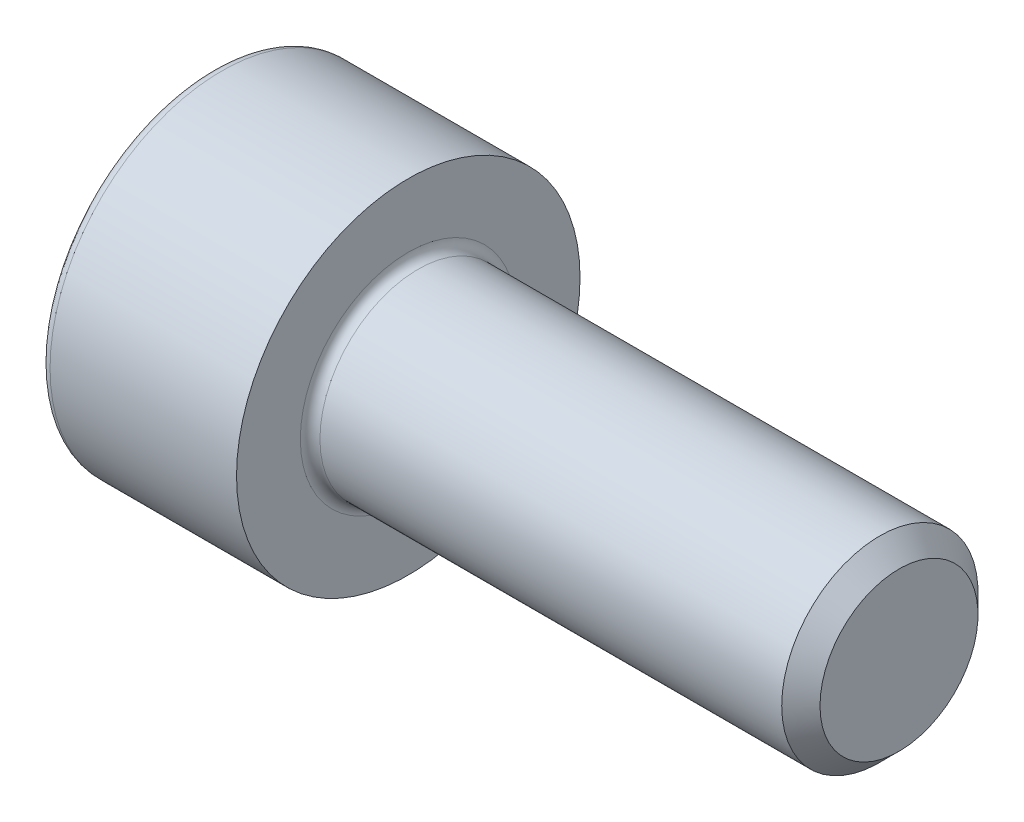
SolidWorks part; units mm, degrees
ref_plane "Front Plane" through (0, 0, 0) normal (0, 0, 1) x (1, 0, 0)
ref_plane "Top Plane" through (0, 0, 0) normal (0, 1, 0) x (1, 0, 0)
ref_plane "Right Plane" through (0, 0, 0) normal (1, 0, 0) x (0, 0, -1)
sketch "BodySke" plane through (0, 0, 0) normal (0, 0, 1) x (1, 0, 0)
  line L0 (0, 0) -> (5.8492, 0) construction
  line L1 (0, 0) -> (0, 3.5)
  line L2 (0, 3.5) -> (4, 3.5)
  line L3 (4, 3.5) -> (4, 2)
  line L4 (4, 2) -> (13.61, 2)
  line L5 (13.61, 2) -> (14, 1.61)
  line L6 (14, 1.61) -> (14, 0)
  line L7 (14, 0) -> (0, 0)
  line L8 (4, 0) -> (4, 0.601) construction
  line L9 (4.7, 1.5877) -> (4.7, 0.9267) construction
  dimension "Body_chamfer_angle" = 45
revolve "BaseBody" add sketch "BodySke" angle 360 about L0
cosmetic thread "ThreadCosmetic" [suppressed] parameters "Thread_length"=10, "Thread_minor"=3.22
fillet "Fillet1" radius 0.2 1 edges at (4, 0, 2)
fillet "Fillet2" radius 0.2 1 edges at (0, 0, 3.5)
sketch "HexSke" plane through (0, 0, 0) normal (1, 0, 0) x (0, 0, -1)
  line L1 (0, 1.7321) -> (-1.5, 0.866)
  line L2 (-1.5, 0.866) -> (-1.5, -0.866)
  line L3 (-1.5, -0.866) -> (0, -1.7321)
  line L4 (0, -1.7321) -> (1.5, -0.866)
  line L5 (1.5, -0.866) -> (1.5, 0.866)
  line L6 (1.5, 0.866) -> (0, 1.7321)
  circle A0 centre (0, 0) radius 1.5 construction
extrude "Hex" cut sketch "HexSke" along normal blind 2
sketch "Hex-PreBroachSke" plane through (0, 0, 0) normal (0, 0, 1) x (1, 0, 0)
  line L0 (0, 0) -> (4.7325, 0) construction
  line L1 (0, 3.3) -> (0, -3.3) construction
  line L2 (0, 0) -> (0, 1.5)
  line L3 (0, 1.5) -> (2, 1.5)
  line L4 (2, 1.5) -> (2.866, 0)
  line L5 (2.866, 0) -> (0, 0)
  dimension "Angle" = 60
revolve "Hex-PreBroach" cut sketch "Hex-PreBroachSke" angle 360 about L0
sketch "ThdSchSke" plane through (0, 0, 0) normal (0, 0, 1) x (1, 0, 0)
  line L0 (0, 0) -> (4.4125, 0) construction
  line L1 (0, 3.3) -> (0, -3.3) construction
  line L2 (12.91, 2.4503) -> (12.91, 2)
  line L3 (12.91, 2.4503) -> (13.3603, 2.4503)
  line L4 (13.3603, 2.4503) -> (13.3603, 2)
  line L5 (13.3603, 2) -> (13.1352, 1.61)
  line L6 (13.1352, 1.61) -> (12.91, 2)
revolve "ThreadSchematic" [suppressed] cut sketch "ThdSchSke" angle 360 about L0
pattern_linear "ThdSchPat" [suppressed]
equation "\"Thread_length@ThreadCosmetic\" = \"Thread_length@BodySke\""
equation "\"Thread_minor@ThreadCosmetic\" = \"Thread_minor@BodySke\""
equation "\"Hex_depth@Hex-PreBroachSke\" = \"Hex_length@Hex\""
equation "\"D1@Hex-PreBroachSke\" = \"Hex_size@HexSke\""
equation "\"D1@ThdSchSke\" = \"Advance@BodySke\""
equation "\"Advance@ThdSchPat\" = \"Advance@BodySke\""
equation "\"Tooth_Num@ThdSchPat\" =  int( \"Thread_length@BodySke\" / \"Advance@BodySke\" )  - 1"
